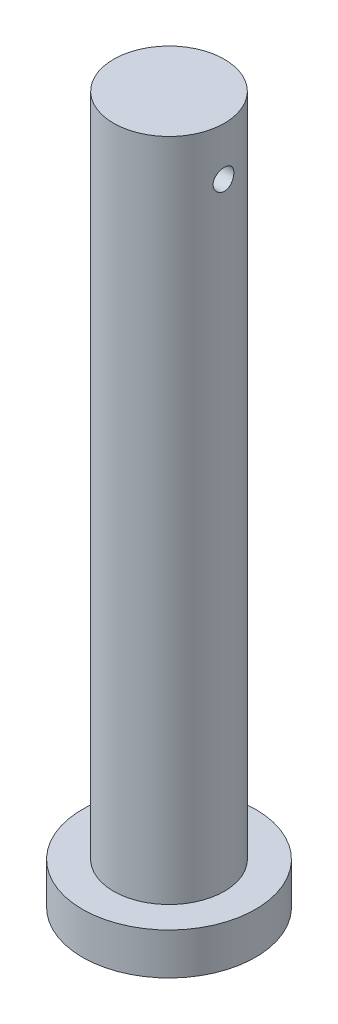
SolidWorks part; units mm, degrees
material "AISI 1020"
ref_plane "Front Plane" through (0, 0, 0) normal (0, 0, 1) x (1, 0, 0)
ref_plane "Top Plane" through (0, 0, 0) normal (0, 1, 0) x (1, 0, 0)
ref_plane "Right Plane" through (0, 0, 0) normal (1, 0, 0) x (0, 0, -1)
sketch "Sketch1" plane through (0, 0, 0) normal (0, 1, 0) x (1, 0, 0)
  circle A0 centre (0, 0) radius 12.5
  dimension "D1" = 25
extrude "Boss-Extrude1" add sketch "Sketch1" along normal mid plane 6
sketch "Sketch2" plane through (0, 3, 0) normal (0, 1, 0) x (1, 0, 0)
  circle A0 centre (0, 0) radius 8
  dimension "D1" = 16
extrude "Boss-Extrude2" add sketch "Sketch2" along normal blind 96
sketch "Sketch4" plane through (0, 0, 0) normal (0, 0, 1) x (1, 0, 0)
  line L0 (12.5, 3) -> (-12.5, 3) construction
  point P0 (0, 92)
  dimension "D1" = 89
ref_plane "Plane1" through (0, 0, 8) normal (0, 0, 1) x (1, 0, 0)
sketch "Sketch5" plane through (0, 0, 0) normal (1, 0, 0) x (0, 0, -1)
  circle A0 centre (0, 92) radius 1.5
  dimension "D1" = 3
  dimension "D2" = 89
extrude "Cut-Extrude1" cut sketch "Sketch5" against normal through all both and the other way through all
scale "Scale1" scale about centroid uniform scaling yes scale factor 2
